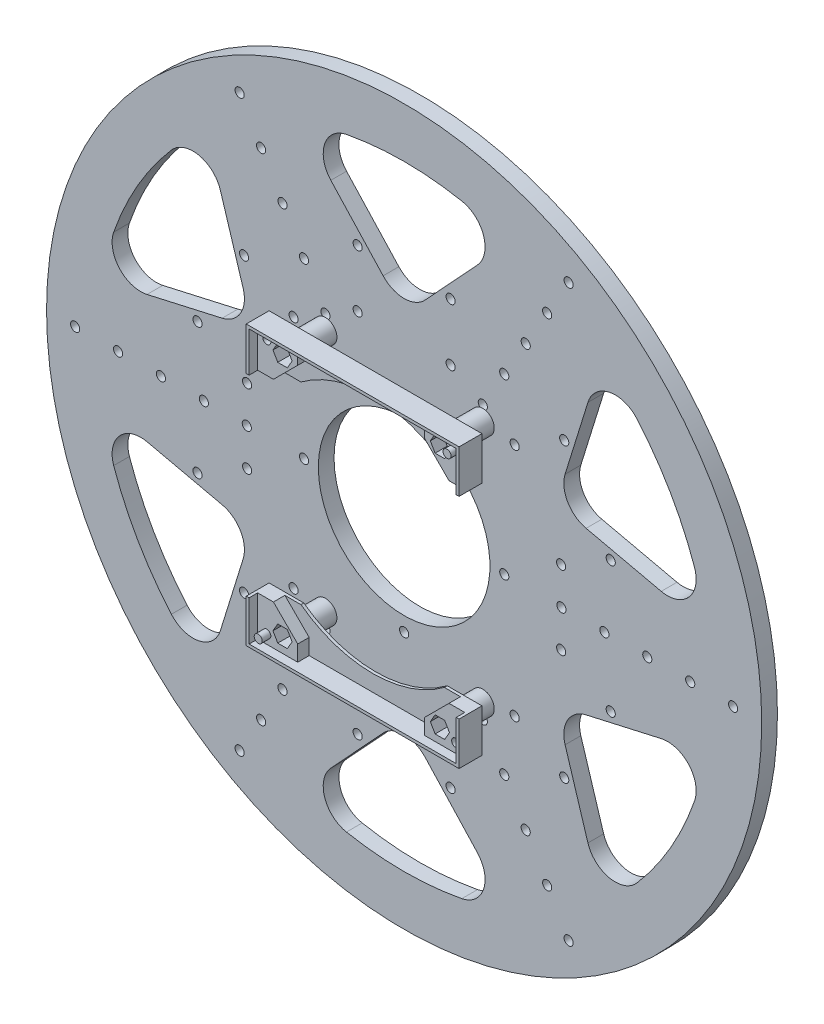
SolidWorks part; units mm, degrees
material "ﾎﾟﾘｴﾁﾚﾝﾃﾚﾌﾀﾗｰﾄ(PET)"
ref_plane "正面" through (0, 0, 0) normal (0, 0, 1) x (1, 0, 0)
ref_plane "平面" through (0, 0, 0) normal (0, 1, 0) x (1, 0, 0)
ref_plane "右側面" through (0, 0, 0) normal (1, 0, 0) x (0, 0, -1)
sketch "ｽｹｯﾁ1" plane through (0, 0, 0) normal (0, 0, 1) x (1, 0, 0)
  circle A0 centre (0, 0) radius 125
  dimension "D1" = 250
extrude "ﾎﾞｽ - 押し出し1" add sketch "ｽｹｯﾁ1" along normal blind 5.5
sketch "ｽｹｯﾁ2" plane through (0, 0, 0) normal (0, 1, 0) x (1, 0, 0)
  line L0 (0, 0) -> (0, -50)
  dimension "D1" = 50
sketch "ｽｹｯﾁ3" plane through (0, 0, 0) normal (0, 0, -1) x (-1, 0, 0)
  line L0 (0, 0) -> (0, 64) construction
  line L1 (0, 0) -> (0, 76) construction
  line L2 (16.25, 54) -> (-16.25, 54) construction
  line L3 (16.25, 54) -> (16.25, 74) construction
  line L4 (16.25, 74) -> (-16.25, 74) construction
  line L5 (-16.25, 54) -> (-16.25, 74) construction
  line L6 (16.25, 54) -> (-16.25, 74) construction
  line L7 (16.25, 74) -> (-16.25, 54) construction
  line L8 (0, 107.5) -> (0, 0) construction
  line L9 (0, 0) -> (36.7672, 101.017) construction
  line L10 (0, 0) -> (-36.7672, 101.017) construction
  line L11 (-25.6298, 88.9783) -> (-7.3405, 69.209)
  line L12 (25.6298, 88.9783) -> (7.3405, 69.209)
  circle A0 centre (-16.25, 74) radius 1.6
  circle A1 centre (-16.25, 54) radius 1.6
  circle A2 centre (16.25, 54) radius 1.6
  circle A3 centre (16.25, 74) radius 1.6
  circle A4 centre (0, 76) radius 10 construction
  circle A5 centre (0, 0) radius 107.5 construction
  arc A6 (-20.1651, 105.5918) -> (20.1651, 105.5918) centre (0, 0) cw
  arc A7 (-7.3405, 69.209) -> (7.3405, 69.209) centre (0, 76) ccw
  arc A8 (-25.6298, 88.9783) -> (-20.1651, 105.5918) centre (-18.2893, 95.7693) cw
  arc A9 (20.1651, 105.5918) -> (25.6298, 88.9783) centre (18.2893, 95.7693) cw
  dimension "D4" = 3.2
  dimension "D6" = 20
  dimension "D7" = 215
  dimension "D10" = 10
  dimension "D1" = 54
  dimension "D2" = 32.5
  dimension "D3" = 20
  dimension "D5" = 76
  dimension "D8" = 20
  dimension "D9" = 20
extrude "ｶｯﾄ - 押し出し1" cut sketch "ｽｹｯﾁ3" against normal through all
pattern_circular "円形ﾊﾟﾀｰﾝ1" count 6 over 360 about axis through (0, 0, 0) along (0, 0, 1) of "ｶｯﾄ - 押し出し1"
sketch "ｽｹｯﾁ4" plane through (0, 0, 0) normal (0, 0, -1) x (-1, 0, 0)
  circle A0 centre (0, 0) radius 30
  circle A1 centre (0, 0) radius 35 construction
  circle A2 centre (0, 35) radius 1.6
  circle A3 centre (35, 0) radius 1.6
  circle A4 centre (0, -35) radius 1.6
  circle A5 centre (-35, 0) radius 1.6
  point P15 (0, 0)
  dimension "D1" = 60
  dimension "D2" = 70
  dimension "D3" = 3.2
  dimension "D4" = 4
extrude "ｶｯﾄ - 押し出し2" cut sketch "ｽｹｯﾁ4" against normal through all
sketch "ｽｹｯﾁ5" plane through (0, 0, 0) normal (0, 0, -1) x (-1, 0, 0)
  line L1 (27.5, -42.5) -> (-27.5, -42.5) construction
  line L2 (27.5, -42.5) -> (27.5, 42.5) construction
  line L3 (27.5, 42.5) -> (-27.5, 42.5) construction
  line L4 (-27.5, -42.5) -> (-27.5, 42.5) construction
  line L5 (27.5, -42.5) -> (-27.5, 42.5) construction
  line L6 (27.5, 42.5) -> (-27.5, -42.5) construction
  circle A0 centre (-27.5, 42.5) radius 1.6
  circle A1 centre (27.5, 42.5) radius 1.6
  circle A2 centre (-27.5, -42.5) radius 1.6
  circle A3 centre (27.5, -42.5) radius 1.6
  point P0 (0, 0)
  dimension "D3" = 3.2
  dimension "D1" = 55
  dimension "D2" = 85
extrude "ｶｯﾄ - 押し出し3" cut sketch "ｽｹｯﾁ5" against normal through all
sketch "ｽｹｯﾁ6" plane through (0, 0, 0) normal (0, 0, -1) x (-1, 0, 0)
  line L0 (-115, 0) -> (0, 0) construction
  line L1 (-57.5, 99.5929) -> (0, 0) construction
  line L2 (57.5, 99.5929) -> (0, 0) construction
  line L3 (115, 0) -> (0, 0) construction
  line L4 (57.5, -99.5929) -> (0, 0) construction
  line L5 (-57.5, -99.5929) -> (0, 0) construction
  circle A0 centre (0, 0) radius 115 construction
  circle A1 centre (-115, 0) radius 1.6
  circle A2 centre (0, 0) radius 125 construction
  circle A3 centre (-100, 0) radius 1.6
  circle A4 centre (-85, 0) radius 1.6
  circle A5 centre (-70, 0) radius 1.6
  circle A6 centre (-55, 0) radius 1.6
  circle A7 centre (-57.5, 99.5929) radius 1.6
  circle A8 centre (-50, 86.6025) radius 1.6
  circle A9 centre (-42.5, 73.6122) radius 1.6
  circle A10 centre (-35, 60.6218) radius 1.6
  circle A11 centre (-27.5, 47.6314) radius 1.6
  circle A12 centre (57.5, 99.5929) radius 1.6
  circle A13 centre (50, 86.6025) radius 1.6
  circle A14 centre (42.5, 73.6122) radius 1.6
  circle A15 centre (35, 60.6218) radius 1.6
  circle A16 centre (27.5, 47.6314) radius 1.6
  circle A17 centre (115, 0) radius 1.6
  circle A18 centre (100, 0) radius 1.6
  circle A19 centre (85, 0) radius 1.6
  circle A20 centre (70, 0) radius 1.6
  circle A21 centre (55, 0) radius 1.6
  circle A22 centre (57.5, -99.5929) radius 1.6
  circle A23 centre (50, -86.6025) radius 1.6
  circle A24 centre (42.5, -73.6122) radius 1.6
  circle A25 centre (35, -60.6218) radius 1.6
  circle A26 centre (27.5, -47.6314) radius 1.6
  circle A27 centre (-57.5, -99.5929) radius 1.6
  circle A28 centre (-50, -86.6025) radius 1.6
  circle A29 centre (-42.5, -73.6122) radius 1.6
  circle A30 centre (-35, -60.6218) radius 1.6
  circle A31 centre (-27.5, -47.6314) radius 1.6
  point P68 (0, 0)
  dimension "D1" = 3.2
  dimension "D2" = 10
  dimension "D3" = 5
  dimension "D4" = 15
  dimension "D5" = 6
extrude "ｶｯﾄ - 押し出し4" cut sketch "ｽｹｯﾁ6" against normal through all
sketch "ｽｹｯﾁ7" plane through (0, 0, 5.5) normal (0, 0, -1) x (-1, 0, 0)
  circle A0 centre (-27.5, -42.5) radius 1.8
  circle A1 centre (27.5, -42.5) radius 1.8
  circle A2 centre (27.5, 42.5) radius 1.8
  circle A3 centre (-27.5, 42.5) radius 1.8
  circle A4 centre (-27.5, 42.5) radius 4
  circle A5 centre (27.5, 42.5) radius 4
  circle A6 centre (-27.5, -42.5) radius 4
  circle A7 centre (27.5, -42.5) radius 4
  dimension "D1" = 3.6
  dimension "D2" = 8
extrude "ﾎﾞｽ - 押し出し2" add sketch "ｽｹｯﾁ7" against normal blind 10 separate body
sketch "ｽｹｯﾁ8" plane through (0, 0, 15.5) normal (0, 0, 1) x (1, 0, 0)
  line L0 (37.2, -48.7) -> (-37.2, -48.7)
  line L1 (36, -47.5) -> (-36, -47.5) construction
  line L2 (36, -47.5) -> (36, 47.5) construction
  line L3 (36, 47.5) -> (-36, 47.5) construction
  line L4 (-36, -47.5) -> (-36, 47.5) construction
  line L5 (36, -47.5) -> (-36, 47.5) construction
  line L6 (36, 47.5) -> (-36, -47.5) construction
  line L7 (33, -44.5) -> (-33, -44.5) construction
  line L8 (33, -44.5) -> (33, 44.5) construction
  line L9 (33, 44.5) -> (-33, 44.5) construction
  line L10 (-33, -44.5) -> (-33, 44.5) construction
  line L11 (33, -44.5) -> (-33, 44.5) construction
  line L12 (33, 44.5) -> (-33, -44.5) construction
  line L13 (-37.2, -48.7) -> (-37.2, 48.7) construction
  line L14 (37.2, 48.7) -> (-37.2, 48.7)
  line L15 (37.2, -48.7) -> (37.2, 48.7) construction
  line L16 (-37.2, 48.7) -> (-37.2, 33.7)
  line L17 (-37.2, 33.7) -> (-25.0661, 33.7)
  line L18 (25.0661, 33.7) -> (37.2, 33.7)
  line L19 (37.2, 33.7) -> (37.2, 48.7)
  line L20 (8.525, 0) -> (-8.525, 0) construction
  line L21 (37.2, -33.7) -> (37.2, -48.7)
  line L22 (25.0661, -33.7) -> (37.2, -33.7)
  line L23 (-37.2, -33.7) -> (-25.0661, -33.7)
  line L24 (-37.2, -48.7) -> (-37.2, -33.7)
  arc A0 (-25.0661, 33.7) -> (25.0661, 33.7) centre (0, 0) cw
  arc A1 (-25.0661, -33.7) -> (25.0661, -33.7) centre (0, 0) ccw
  point P0 (0, 0)
  point P6 (0, 0)
  dimension "D6" = 42
  dimension "D1" = 95
  dimension "D2" = 72
  dimension "D3" = 66
  dimension "D4" = 89
  dimension "D7" = 15
  dimension "D5" = 1.2
extrude "ﾎﾞｽ - 押し出し3" add sketch "ｽｹｯﾁ8" along normal blind 1
sketch "ｽｹｯﾁ10" plane through (0, 0, 16.5) normal (0, 0, 1) x (1, 0, 0)
  line L0 (37.2, 33.7) -> (37.2, 48.7) construction
  line L1 (37.2, 48.7) -> (-37.2, 48.7) construction
  line L2 (-37.2, 48.7) -> (-37.2, 33.7) construction
  line L3 (37.2, 33.7) -> (37.2, 48.7)
  line L4 (37.2, 48.7) -> (-37.2, 48.7)
  line L5 (-37.2, 48.7) -> (-37.2, 33.7)
  line L6 (36.2, 33.7) -> (36.2, 47.7)
  line L7 (36.2, 47.7) -> (-36.2, 47.7)
  line L8 (-36.2, 47.7) -> (-36.2, 33.7)
  line L9 (-37.2, 33.7) -> (-36.2, 33.7)
  line L10 (36.2, 33.7) -> (37.2, 33.7)
  line L11 (8.525, 0) -> (-8.525, 0) construction
  line L12 (36.2, -33.7) -> (37.2, -33.7)
  line L13 (-37.2, -33.7) -> (-36.2, -33.7)
  line L14 (-36.2, -47.7) -> (-36.2, -33.7)
  line L15 (36.2, -47.7) -> (-36.2, -47.7)
  line L16 (36.2, -33.7) -> (36.2, -47.7)
  line L17 (-37.2, -48.7) -> (-37.2, -33.7)
  line L18 (37.2, -48.7) -> (-37.2, -48.7)
  line L19 (37.2, -33.7) -> (37.2, -48.7)
  dimension "D1" = 1
extrude "ﾎﾞｽ - 押し出し4" add sketch "ｽｹｯﾁ10" along normal blind 7
sketch "ｽｹｯﾁ11" plane through (0, 0, 16.5) normal (0, 0, 1) x (1, 0, 0)
  line L0 (-36.2, 47.7) -> (-36.2, 33.7)
  line L1 (-36.2, 33.7) -> (-30.6853, 33.7)
  line L2 (-37.2, 33.7) -> (-25.0661, 33.7) construction
  line L3 (-36.2, 47.7) -> (-22.2, 47.7)
  line L4 (-36.2, 47.7) -> (36.2, 47.7) construction
  line L5 (-22.2, 47.7) -> (-22.2, 42.1853)
  line L6 (-22.2, 42.1853) -> (-30.6853, 33.7)
  line L7 (0, -9.075) -> (0, 9.075) construction
  line L8 (22.2, 42.1853) -> (30.6853, 33.7)
  line L9 (22.2, 47.7) -> (22.2, 42.1853)
  line L10 (36.2, 47.7) -> (22.2, 47.7)
  line L11 (36.2, 33.7) -> (30.6853, 33.7)
  line L12 (36.2, 47.7) -> (36.2, 33.7)
  line L13 (9.075, 0) -> (-9.075, 0) construction
  line L14 (36.2, -47.7) -> (36.2, -33.7)
  line L15 (36.2, -33.7) -> (30.6853, -33.7)
  line L16 (36.2, -47.7) -> (22.2, -47.7)
  line L17 (22.2, -47.7) -> (22.2, -42.1853)
  line L18 (22.2, -42.1853) -> (30.6853, -33.7)
  line L19 (-22.2, -42.1853) -> (-30.6853, -33.7)
  line L20 (-22.2, -47.7) -> (-22.2, -42.1853)
  line L21 (-36.2, -47.7) -> (-22.2, -47.7)
  line L22 (-36.2, -33.7) -> (-30.6853, -33.7)
  line L23 (-36.2, -47.7) -> (-36.2, -33.7)
  dimension "D1" = 12
extrude "ﾎﾞｽ - 押し出し5" add sketch "ｽｹｯﾁ11" along normal blind 4
sketch "ｽｹｯﾁ12" plane through (0, 0, 20.5) normal (0, 0, 1) x (1, 0, 0)
  circle A0 centre (-33, 44.5) radius 1.4
  circle A1 centre (33, 44.5) radius 1.4
  circle A2 centre (-33, -44.5) radius 1.4
  circle A3 centre (33, -44.5) radius 1.4
  dimension "D1" = 2.8
extrude "ﾎﾞｽ - 押し出し6" add sketch "ｽｹｯﾁ12" along normal blind 3
sketch "ｽｹｯﾁ13" plane through (0, 0, 15.5) normal (0, 0, -1) x (-1, 0, 0)
  line L1 (-29.1743, 39.6) -> (-25.8257, 39.6)
  line L2 (-25.8257, 39.6) -> (-24.1514, 42.5)
  line L3 (-24.1514, 42.5) -> (-25.8257, 45.4)
  line L4 (-25.8257, 45.4) -> (-29.1743, 45.4)
  line L5 (-29.1743, 45.4) -> (-30.8486, 42.5)
  line L6 (-30.8486, 42.5) -> (-29.1743, 39.6)
  line L7 (24.1514, 42.5) -> (25.8257, 39.6)
  line L8 (25.8257, 39.6) -> (29.1743, 39.6)
  line L9 (29.1743, 39.6) -> (30.8486, 42.5)
  line L10 (30.8486, 42.5) -> (29.1743, 45.4)
  line L11 (29.1743, 45.4) -> (25.8257, 45.4)
  line L12 (25.8257, 45.4) -> (24.1514, 42.5)
  line L13 (25.8257, -45.4) -> (29.1743, -45.4)
  line L14 (29.1743, -45.4) -> (30.8486, -42.5)
  line L15 (30.8486, -42.5) -> (29.1743, -39.6)
  line L16 (29.1743, -39.6) -> (25.8257, -39.6)
  line L17 (25.8257, -39.6) -> (24.1514, -42.5)
  line L18 (24.1514, -42.5) -> (25.8257, -45.4)
  line L19 (-30.8486, -42.5) -> (-29.1743, -45.4)
  line L20 (-29.1743, -45.4) -> (-25.8257, -45.4)
  line L21 (-25.8257, -45.4) -> (-24.1514, -42.5)
  line L22 (-24.1514, -42.5) -> (-25.8257, -39.6)
  line L23 (-25.8257, -39.6) -> (-29.1743, -39.6)
  line L24 (-29.1743, -39.6) -> (-30.8486, -42.5)
  circle A0 centre (-27.5, 42.5) radius 2.9 construction
  circle A1 centre (27.5, 42.5) radius 2.9 construction
  circle A2 centre (27.5, -42.5) radius 2.9 construction
  circle A3 centre (-27.5, -42.5) radius 2.9 construction
  dimension "D1" = 5.8
extrude "ｶｯﾄ - 押し出し5" cut sketch "ｽｹｯﾁ13" against normal through all
sketch "ｽｹｯﾁ14" plane through (0, 0, 23.5) normal (0, 0, 1) x (1, 0, 0)
  circle A1 centre (-33, 44.5) radius 1.4
  circle A2 centre (-33, 44.5) radius 1.4
  circle A3 centre (33, -44.5) radius 1.4
  circle A4 centre (33, -44.5) radius 1.4
  dimension "D1" = 0
  dimension "D2" = 0
extrude "ｶｯﾄ - 押し出し6" cut sketch "ｽｹｯﾁ14" against normal through all
equation "\"D1@ｽｹｯﾁ3\"=50+4"
equation "\"D7@ｽｹｯﾁ3\"=107.5*2"
equation "\"D9@ｽｹｯﾁ3\"=\"D8@ｽｹｯﾁ3\""
